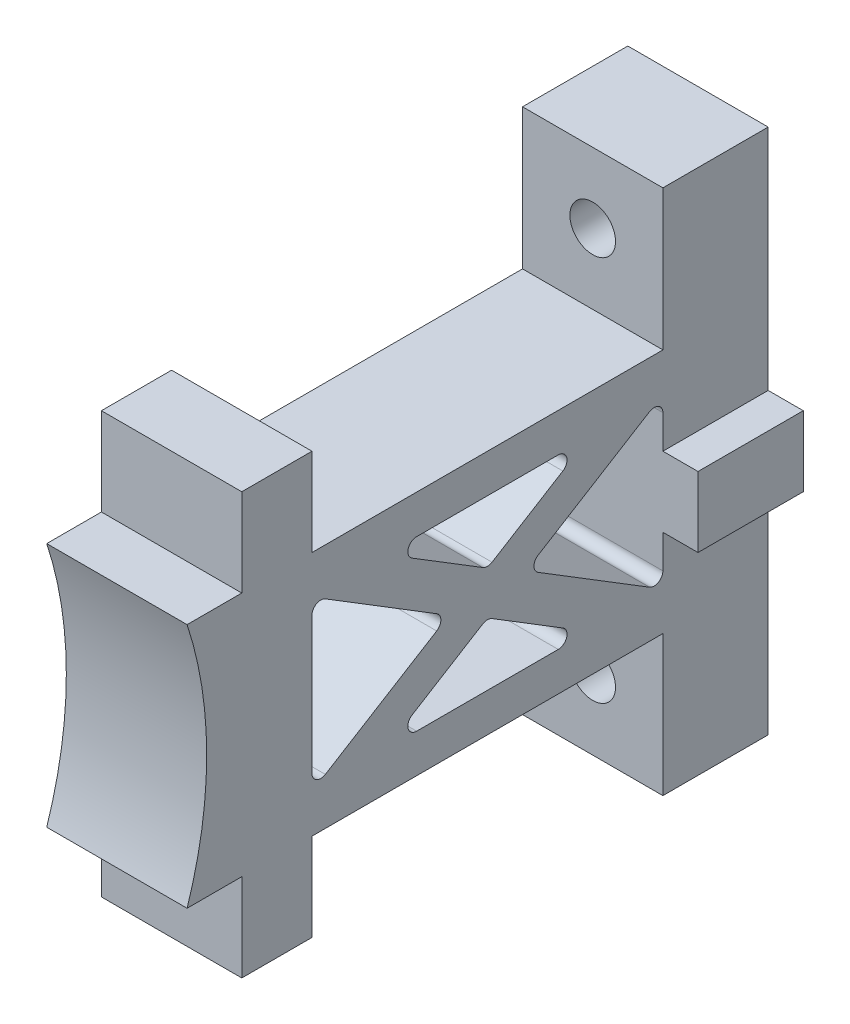
SolidWorks part; units mm, degrees
ref_plane "Front Plane" through (0, 0, 0) normal (0, 0, 1) x (1, 0, 0)
ref_plane "Top Plane" through (0, 0, 0) normal (0, 1, 0) x (1, 0, 0)
ref_plane "Right Plane" through (0, 0, 0) normal (1, 0, 0) x (0, 0, -1)
sketch "Sketch1" plane through (0, 0, 0) normal (1, 0, 0) x (0, 0, -1)
  line L0 (57.15, 0) -> (138.43, 0) construction
  line L2 (54.3138, 17.78) -> (62.23, 17.78)
  line L3 (62.23, 17.78) -> (62.23, 30.48)
  line L4 (62.23, 30.48) -> (72.39, 30.48)
  line L5 (72.39, 30.48) -> (72.39, 17.78)
  line L6 (72.39, 17.78) -> (123.19, 17.78)
  line L7 (123.19, 17.78) -> (123.19, 38.1)
  line L8 (123.19, 38.1) -> (138.43, 38.1)
  line L11 (138.43, 38.1) -> (138.43, -38.1)
  line L22 (123.19, -38.1) -> (138.43, -38.1)
  line L23 (123.19, -17.78) -> (123.19, -38.1)
  line L24 (72.39, -17.78) -> (123.19, -17.78)
  line L25 (72.39, -30.48) -> (72.39, -17.78)
  line L26 (62.23, -30.48) -> (72.39, -30.48)
  line L27 (62.23, -17.78) -> (62.23, -30.48)
  line L28 (54.3138, -17.78) -> (62.23, -17.78)
  arc A0 (54.3138, -17.78) -> (54.3138, 17.78) centre (0, 0) ccw
  point P1 (97.79, 17.78)
  point P6 (97.79, -17.78)
  dimension "D1" = 114.3
  dimension "D3" = 17.78
  dimension "D2" = 5.08
  dimension "D4" = 10.16
  dimension "D5" = 30.48
  dimension "D6" = 50.8
  dimension "D7" = 38.1
  dimension "D8" = 15.24
extrude "Boss-Extrude1" add sketch "Sketch1" along normal mid plane 20.32
sketch "Sketch2" plane through (10.16, 0, 0) normal (1, 0, 0) x (0, 0, -1)
  line L0 (72.39, 9.9193) -> (72.39, -9.9193)
  line L1 (72.39, -17.78) -> (123.19, -17.78) construction
  line L2 (74.3256, -11.0009) -> (90.4444, -1.0816)
  line L3 (90.4444, 1.0816) -> (74.3256, 11.0009)
  line L4 (123.19, 9.9193) -> (123.19, -9.9193)
  line L5 (121.2544, -11.0009) -> (105.1356, -1.0816)
  line L6 (105.1356, 1.0816) -> (121.2544, 11.0009)
  line L7 (92.202, 0) -> (72.39, 0) construction
  line L8 (103.378, 0) -> (123.19, 0) construction
  line L9 (86.8735, 9.8404) -> (97.1244, 3.5321)
  line L10 (108.7065, 9.8404) -> (98.4556, 3.5321)
  line L11 (87.5391, 12.192) -> (108.0409, 12.192)
  line L12 (87.5391, -12.192) -> (108.0409, -12.192)
  line L13 (108.7065, -9.8404) -> (98.4556, -3.5321)
  line L14 (86.8735, -9.8404) -> (97.1244, -3.5321)
  arc A0 (123.19, 9.9193) -> (121.2544, 11.0009) centre (121.92, 9.9193) ccw
  arc A1 (123.19, -9.9193) -> (121.2544, -11.0009) centre (121.92, -9.9193) cw
  arc A2 (108.0409, -12.192) -> (108.7065, -9.8404) centre (108.0409, -10.922) ccw
  arc A3 (98.4556, -3.5321) -> (97.1244, -3.5321) centre (97.79, -4.6138) ccw
  arc A4 (87.5391, -12.192) -> (86.8735, -9.8404) centre (87.5391, -10.922) cw
  arc A5 (72.39, -9.9193) -> (74.3256, -11.0009) centre (73.66, -9.9193) ccw
  arc A6 (72.39, 9.9193) -> (74.3256, 11.0009) centre (73.66, 9.9193) cw
  arc A7 (108.7065, 9.8404) -> (108.0409, 12.192) centre (108.0409, 10.922) ccw
  arc A8 (86.8735, 9.8404) -> (87.5391, 12.192) centre (87.5391, 10.922) cw
  arc A9 (98.4556, 3.5321) -> (97.1244, 3.5321) centre (97.79, 4.6138) cw
  arc A10 (105.1356, -1.0816) -> (105.1356, 1.0816) centre (105.8012, 0) cw
  arc A11 (90.4444, -1.0816) -> (90.4444, 1.0816) centre (89.7788, 0) ccw
  point P8 (72.39, 0)
  point P21 (123.19, 12.192)
  point P26 (112.5279, -12.192)
  point P29 (97.79, -3.1225)
  point P32 (83.0521, -12.192)
  point P35 (72.39, -12.192)
  point P38 (72.39, 12.192)
  point P41 (112.5279, 12.192)
  point P44 (83.0521, 12.192)
  point P47 (97.79, 3.1225)
  dimension "D6" = 1.27
  dimension "D1" = 5.588
  dimension "D2" = 5.588
  dimension "D3" = 5.588
  dimension "D4" = 5.588
  dimension "D5" = 11.176
extrude "Cut-Extrude1" cut sketch "Sketch2" against normal through all
sketch "Sketch3" plane through (0, 0, -123.19) normal (0, 0, 1) x (1, 0, 0)
  line L1 (10.16, 17.78) -> (-10.16, 17.78) construction
  line L2 (-10.16, 38.1) -> (-10.16, 17.78) construction
  line L4 (0, 0) -> (10.16, 0) construction
  line L5 (10.16, -9.9193) -> (10.16, 9.9193) construction
  circle A0 centre (0, 27.94) radius 3.302
  circle A1 centre (0, -27.94) radius 3.302
  dimension "D1" = 6.604
  dimension "D2" = 10.16
  dimension "D3" = 10.16
extrude "Cut-Extrude2" cut sketch "Sketch3" against normal through all
sketch "Sketch4" plane through (10.16, 0, 0) normal (1, 0, 0) x (0, 0, -1)
  line L0 (123.19, -9.9193) -> (123.19, 9.9193) construction
  line L1 (123.19, 5.08) -> (138.43, 5.08)
  line L2 (123.19, 5.08) -> (123.19, -5.08)
  line L3 (123.19, -5.08) -> (138.43, -5.08)
  line L4 (138.43, 5.08) -> (138.43, -5.08)
  line L5 (138.43, -38.1) -> (138.43, 38.1) construction
  line L6 (123.19, 0) -> (138.43, 0) construction
  line L7 (132.9977, 0) -> (132.9977, 5.08) construction
  line L8 (132.9977, 0) -> (132.9977, -5.08) construction
  line L9 (129.0133, 0) -> (129.0133, -38.1) construction
  line L10 (123.19, -38.1) -> (138.43, -38.1) construction
  line L11 (129.0133, 0) -> (129.0133, 38.1) construction
  line L12 (138.43, 38.1) -> (123.19, 38.1) construction
  dimension "D1" = 10.16
extrude "Boss-Extrude2" add sketch "Sketch4" along normal blind 5.08
